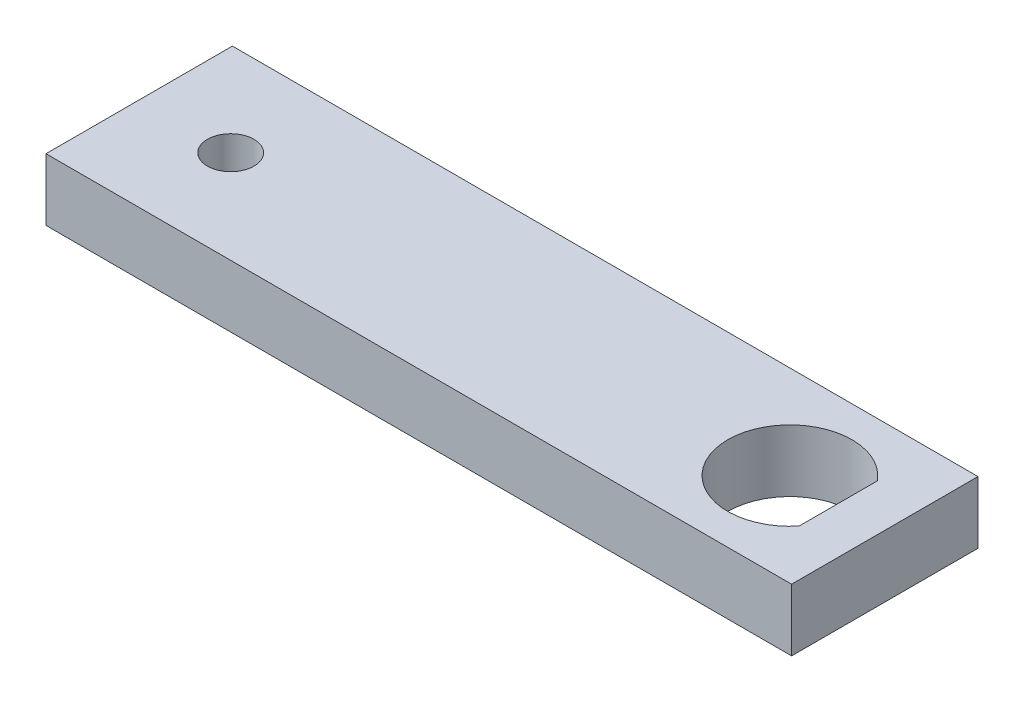
SolidWorks part; units mm, degrees
ref_plane "Front Plane" through (0, 0, 0) normal (0, 0, 1) x (1, 0, 0)
ref_plane "Top Plane" through (0, 0, 0) normal (0, 1, 0) x (1, 0, 0)
ref_plane "Right Plane" through (0, 0, 0) normal (1, 0, 0) x (0, 0, -1)
sketch "Sketch1" plane through (0, 0, 0) normal (0, 1, 0) x (1, 0, 0)
  line L0 (-46.5605, 9.525) -> (49.5226, 9.525) construction
  line L1 (-38.1, 0) -> (38.1, 0)
  line L2 (-38.1, 0) -> (-38.1, 19.05)
  line L3 (-38.1, 19.05) -> (38.1, 19.05)
  line L4 (38.1, 0) -> (38.1, 19.05)
  line L5 (33.34, 13.5148) -> (33.34, 5.5352)
  circle A2 centre (-28.75, 9.525) radius 2.38
  arc A3 (33.34, 13.5148) -> (33.34, 5.5352) centre (28.4, 9.525) ccw
  point P4 (0, 0)
  dimension "D3" = 9.35
  dimension "D5" = 4.76
  dimension "D6" = 12.7
  dimension "D1" = 19.05
  dimension "D2" = 76.2
  dimension "D4" = 9.7
  dimension "D7" = 4.76
extrude "Boss-Extrude1" add sketch "Sketch1" along normal blind 6.35
